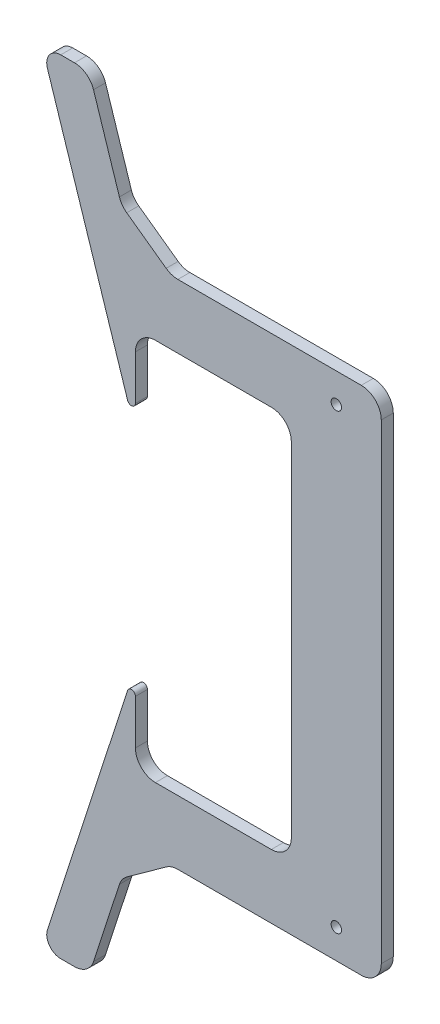
SolidWorks part; units mm, degrees
material "MDF"
ref_plane "Plano frontal" through (0, 0, 0) normal (0, 0, 1) x (1, 0, 0)
ref_plane "Plano superior" through (0, 0, 0) normal (0, 1, 0) x (1, 0, 0)
ref_plane "Plano direito" through (0, 0, 0) normal (1, 0, 0) x (0, 0, -1)
sketch "Esboço1" plane through (0, 0, 0) normal (0, 0, 1) x (1, 0, 0)
  line L0 (-22.5, 127.8) -> (-107.5, 127.8)
  line L1 (-22.5, -127.8) -> (22.5, -127.8)
  line L2 (-22.5, -127.8) -> (-22.5, 127.8)
  line L3 (-22.5, 127.8) -> (22.5, 127.8)
  line L4 (22.5, -127.8) -> (22.5, 127.8)
  line L5 (-22.5, -127.8) -> (22.5, 127.8) construction
  line L6 (-22.5, 127.8) -> (22.5, -127.8) construction
  line L7 (0, 0) -> (22.5, 0) construction
  line L8 (-147.5, 195.8) -> (-100.5, 50.8)
  line L9 (-100.5, 50.8) -> (-22.5, 50.8)
  line L10 (-107.5, 127.8) -> (-107.5, 195.8)
  line L11 (-147.5, -195.8) -> (-100.5, -50.8)
  line L12 (-100.5, -50.8) -> (-22.5, -50.8)
  line L13 (-100.5, 50.8) -> (-100.5, 95.8)
  line L14 (-100.5, 95.8) -> (-22.5, 95.8)
  line L15 (-22.5, 95.8) -> (-22.5, 50.8)
  line L16 (-22.5, -95.8) -> (-22.5, -50.8)
  line L17 (-100.5, -50.8) -> (-100.5, -95.8)
  line L18 (-100.5, -95.8) -> (-22.5, -95.8)
  line L19 (-107.5, 195.8) -> (-147.5, 195.8)
  line L20 (-107.5, -195.8) -> (-147.5, -195.8)
  line L21 (-22.5, -127.8) -> (-107.5, -127.8)
  line L22 (-107.5, -127.8) -> (-107.5, -195.8)
  line L23 (-107.5, 145.8) -> (-82.5, 127.8)
  line L24 (-107.5, -145.8) -> (-82.5, -127.8)
  line L25 (-107.5, 145.8) -> (-123.7069, 195.8)
  line L26 (-107.5, -145.8) -> (-123.7069, -195.8)
  circle A1 centre (0, 113.2) radius 2.6
  circle A2 centre (0, -113.2) radius 2.6
  point P0 (0, 0)
  point P11 (0, 127.8)
  dimension "D2" = 14.6
  dimension "D3" = 5.2
  dimension "D1" = 255.6
  dimension "D4" = 45
  dimension "D5" = 125
  dimension "D6" = 78
  dimension "D7" = 85
  dimension "D8" = 145
  dimension "D9" = 77
  dimension "D10" = 45
  dimension "D11" = 50
  dimension "D12" = 25
extrude "Ressalto-extrusão1" add sketch "Esboço1" along normal blind 6
fillet "Filete1" radius 2 2 edges at (-100.5, -50.8, 3) (-100.5, 50.8, 3)
fillet "Filete3" radius 10 12 edges at (-82.5, -127.8, 3) (-107.5, -145.8, 3) (-123.7069, -195.8, 3) (-100.5, -95.8, 3) (-22.5, -95.8, 3) (22.5, -127.8, 3) (22.5, 127.8, 3) (-22.5, 95.8, 3) (-100.5, 95.8, 3) (-82.5, 127.8, 3) (-107.5, 145.8, 3) (-123.7069, 195.8, 3)
fillet "Filete4" radius 7 2 edges at (-147.5, 195.8, 3) (-147.5, -195.8, 3)
